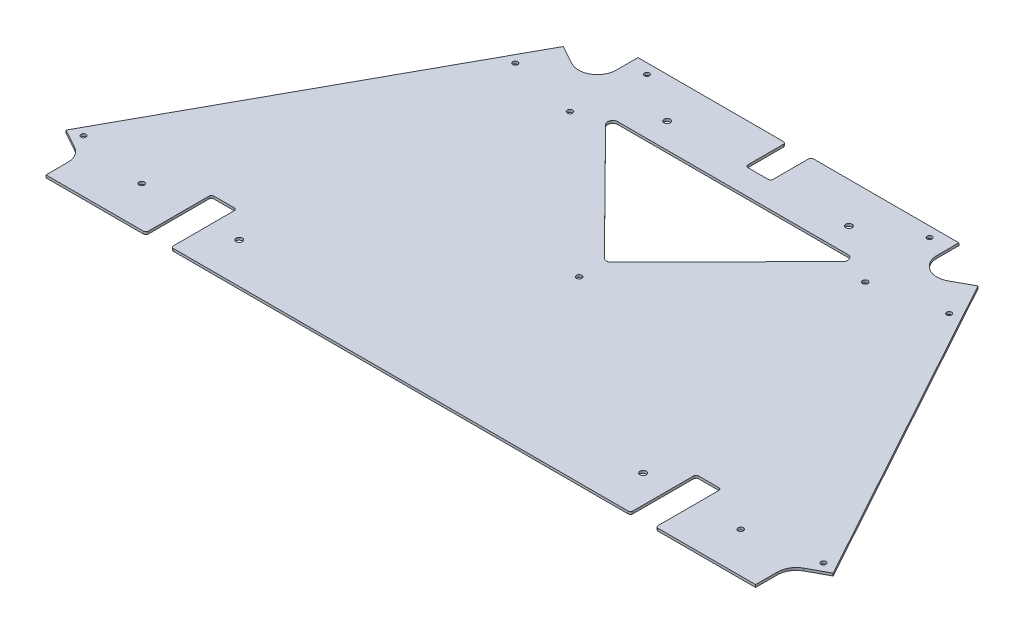
SolidWorks part; units mm, degrees
material "PC High Viscosity"
ref_plane "Front Plane" through (0, 0, 0) normal (0, 0, 1) x (1, 0, 0)
ref_plane "Top Plane" through (0, 0, 0) normal (0, 1, 0) x (1, 0, 0)
ref_plane "Right Plane" through (0, 0, 0) normal (1, 0, 0) x (0, 0, -1)
sketch "Sketch1" plane through (0, 0, 0) normal (0, 1, 0) x (1, 0, 0)
  line L0 (-505.5243, 6.35) -> (-237.901, 493.8184) construction
  line L1 (-237.901, 493.8184) -> (237.901, 493.8184) construction
  line L2 (237.901, 493.8184) -> (505.5243, 6.35) construction
  line L3 (505.5243, 6.35) -> (-505.5243, 6.35) construction
  line L4 (-516.2546, 0) -> (-241.6589, 500.1684)
  line L5 (-241.6589, 500.1684) -> (241.6589, 500.1684)
  line L6 (241.6589, 500.1684) -> (516.2546, 0)
  line L7 (516.2546, 0) -> (-516.2546, 0)
  line L8 (-201.803, 472.7364) -> (-201.803, 500.1684)
  line L9 (-236.7931, 452.0297) -> (-260.8395, 465.2314)
  line L10 (-458.5319, 48.1387) -> (-482.5783, 61.3403)
  line L11 (-446.278, 27.432) -> (-446.278, 0)
  line L12 (0, 500.1684) -> (0, 0) construction
  line L13 (446.278, 27.432) -> (446.278, 0)
  line L14 (458.5319, 48.1387) -> (482.5783, 61.3403)
  line L15 (236.7931, 452.0297) -> (260.8395, 465.2314)
  line L16 (201.803, 472.7364) -> (201.803, 500.1684)
  circle A0 centre (-225.425, 472.7364) radius 21.082 construction
  circle A1 centre (225.425, 472.7364) radius 21.082 construction
  circle A2 centre (469.9, 27.432) radius 21.082 construction
  circle A3 centre (-469.9, 27.432) radius 21.082 construction
  circle A4 centre (-225.425, 472.7364) radius 23.622 construction
  circle A5 centre (-469.9, 27.432) radius 23.622 construction
  arc A6 (-458.5319, 48.1387) -> (-446.278, 27.432) centre (-469.9, 27.432) cw
  arc A7 (-236.7931, 452.0297) -> (-201.803, 472.7364) centre (-225.425, 472.7364) ccw
  arc A8 (458.5319, 48.1387) -> (446.278, 27.432) centre (469.9, 27.432) ccw
  arc A9 (236.7931, 452.0297) -> (201.803, 472.7364) centre (225.425, 472.7364) cw
  point P27 (0, 0)
  dimension "D1" = 42.164
  dimension "D2" = 450.85
  dimension "D3" = 508
  dimension "D4" = 939.8
  dimension "D6" = 6.35
  dimension "D7" = 2.54
extrude "Boss-Extrude1" add sketch "Sketch1" along normal blind 3.175 contours L15 A9 L16 L5 L8 A7 L9 L4 L10 A6 L11 L7 L13 A8 L14 L6
sketch "Sketch2" plane through (0, 3.175, 0) normal (0, 1, 0) x (1, 0, 0)
  line L0 (446.278, 0) -> (-446.278, 0) construction
  line L1 (-288.925, 0) -> (-320.675, 0)
  line L2 (-288.925, 0) -> (-288.925, 82.55)
  line L3 (-288.925, 82.55) -> (-320.675, 82.55)
  line L4 (-320.675, 0) -> (-320.675, 82.55)
  line L5 (0, 0) -> (0, 500.1684) construction
  line L6 (-201.803, 500.1684) -> (201.803, 500.1684) construction
  line L7 (288.925, 82.55) -> (320.675, 82.55)
  line L8 (320.675, 0) -> (320.675, 82.55)
  line L9 (288.925, 0) -> (320.675, 0)
  line L10 (288.925, 0) -> (288.925, 82.55)
  point P11 (-304.8, 0)
  dimension "D1" = 31.75
  dimension "D2" = 82.55
  dimension "D3" = 304.8
extrude "Cut-Extrude1" cut sketch "Sketch2" against normal through all
fillet "Fillet1" radius 3.175 8 edges at (288.925, 1.5875, -82.55) (288.925, 1.5875, 0) (320.675, 1.5875, -82.55) (320.675, 1.5875, 0) (-288.925, 1.5875, 0) (-288.925, 1.5875, -82.55) (-320.675, 1.5875, -82.55) (-320.675, 1.5875, 0)
hole_wizard "1/4 (0.25) Diameter Hole1" positions "Sketch5" profile "Sketch6" hole size "1/4" standard "ANSI Inch" end condition through all
sketch "Sketch5" plane through (0, 3.175, 0) normal (0, 1, 0) x (1, 0, 0)
  line L0 (0, 0) -> (0, 500.1684)
  line L1 (-201.803, 500.1684) -> (201.803, 500.1684) construction
  line L3 (-482.5783, 61.3403) -> (-260.8395, 465.2314) construction
  line L4 (-446.278, 0) -> (-516.2546, 0) construction
  line L5 (-516.2546, 0) -> (-482.5783, 61.3403) construction
  line L7 (-465.3948, 66.2501) -> (-476.5274, 72.362) construction
  line L9 (-272.8707, 416.9273) -> (-284.0033, 423.0391) construction
  point P0 (-465.3948, 66.2501)
  point P2 (-272.8707, 416.9273)
  point P4 (-177.8, 487.4684)
  point P38 (465.3948, 66.2501)
  point P39 (272.8707, 416.9273)
  point P40 (177.8, 487.4684)
  dimension "D1" = 12.7
  dimension "D2" = 177.8
  dimension "D3" = 12.7
  dimension "D4" = 12.7
  dimension "D5" = 82.55
  dimension "D6" = 482.6
sketch "Sketch6" plane through (-465.3948, 3.175, -66.2501) normal (1, 0, 0) x (0, 0, 1)
  line L0 (0, 0) -> (0, 3.175)
  line L1 (0, 3.175) -> (3.175, 3.175)
  line L2 (3.175, 3.175) -> (3.175, 0)
  line L5 (3.175, 0) -> (0, 0)
  line L11 (0, -6.35) -> (0, 107.95) construction
  dimension "Thru Hole Dia." = 6.35
  dimension "Thru Hole Depth" = 3.175
hole_wizard "1/4 Clearance Hole1" positions "Sketch7" profile "Sketch8" hole size "1/4" standard "ANSI Inch" end condition through all
sketch "Sketch7" plane through (0, 3.175, 0) normal (0, 1, 0) x (1, 0, 0)
  line L0 (0, 0) -> (0, 500.1684) construction
  line L1 (-201.803, 500.1684) -> (201.803, 500.1684) construction
  line L2 (-323.85, 0) -> (-446.278, 0) construction
  line L3 (285.75, 0) -> (-285.75, 0) construction
  point P7 (-376.682, 50.8)
  point P9 (-185.674, 398.526)
  point P16 (376.682, 50.8)
  point P17 (185.674, 398.526)
  point P18 (0, 224.282)
  dimension "D1" = 50.8
  dimension "D2" = 376.682
  dimension "D3" = 398.526
  dimension "D4" = 185.674
  dimension "D5" = 224.282
sketch "Sketch8" plane through (0, 3.175, -224.282) normal (1, 0, 0) x (0, 0, 1)
  line L0 (0, 0) -> (0, 3.175)
  line L1 (0, 3.175) -> (3.3782, 3.175)
  line L2 (3.3782, 3.175) -> (3.3782, 0)
  line L5 (3.3782, 0) -> (0, 0)
  line L11 (0, -6.35) -> (0, 107.95) construction
  dimension "Thru Hole Dia." = 6.7564
  dimension "Thru Hole Depth" = 3.175
hole_wizard "5/16 (0.3125) Diameter Hole1" positions "Sketch9" profile "Sketch10" hole size "5/16" standard "ANSI Inch" end condition through all
sketch "Sketch9" plane through (0, 3.175, 0) normal (0, 1, 0) x (1, 0, 0)
  line L0 (0, 0) -> (0, 500.1684) construction
  line L1 (-201.803, 500.1684) -> (201.803, 500.1684) construction
  line L3 (285.75, 0) -> (-285.75, 0) construction
  point P0 (-254, 50.8)
  point P2 (-114.3, 449.3684)
  point P13 (254, 50.8)
  point P14 (114.3, 449.3684)
  dimension "D1" = 50.8
  dimension "D2" = 254
  dimension "D3" = 50.8
  dimension "D4" = 114.3
sketch "Sketch10" plane through (-254, 3.175, -50.8) normal (1, 0, 0) x (0, 0, 1)
  line L0 (0, 0) -> (0, 3.175)
  line L1 (0, 3.175) -> (3.9687, 3.175)
  line L2 (3.9687, 3.175) -> (3.9687, 0)
  line L5 (3.9687, 0) -> (0, 0)
  line L11 (0, -6.35) -> (0, 107.95) construction
  dimension "Thru Hole Dia." = 7.9375
  dimension "Thru Hole Depth" = 3.175
sketch "Sketch11" plane through (0, 3.175, 0) normal (0, 1, 0) x (1, 0, 0)
  line L0 (0, 256.032) -> (159.8995, 417.6184)
  line L1 (159.8995, 417.6184) -> (-159.8995, 417.6184)
  line L2 (-159.8995, 417.6184) -> (0, 256.032)
  circle A1 centre (-114.3, 449.3684) radius 3.9687 construction
  circle A2 centre (-185.674, 398.526) radius 3.3782 construction
  dimension "D2" = 31.75
  dimension "D3" = 31.75
  dimension "D4" = 161.5864
extrude "Cut-Extrude2" cut sketch "Sketch11" against normal through all
fillet "Fillet2" radius 6.35 3 edges at (0, 1.5875, -256.032) (159.8995, 1.5875, -417.6184) (-159.8995, 1.5875, -417.6184)
sketch "Sketch12" plane through (0, 3.175, 0) normal (0, 1, 0) x (1, 0, 0)
  line L0 (-201.803, 500.1684) -> (201.803, 500.1684) construction
  line L1 (-15.875, 500.1684) -> (15.875, 500.1684)
  line L2 (-15.875, 500.1684) -> (-15.875, 449.3684)
  line L3 (-15.875, 449.3684) -> (15.875, 449.3684)
  line L4 (15.875, 500.1684) -> (15.875, 449.3684)
  point P6 (0, 500.1684)
  dimension "D1" = 50.8
  dimension "D2" = 31.75
extrude "Cut-Extrude3" cut sketch "Sketch12" against normal through all
fillet "Fillet3" radius 3.175 4 edges at (15.875, 1.5875, -449.3684) (15.875, 1.5875, -500.1684) (-15.875, 1.5875, -449.3684) (-15.875, 1.5875, -500.1684)
